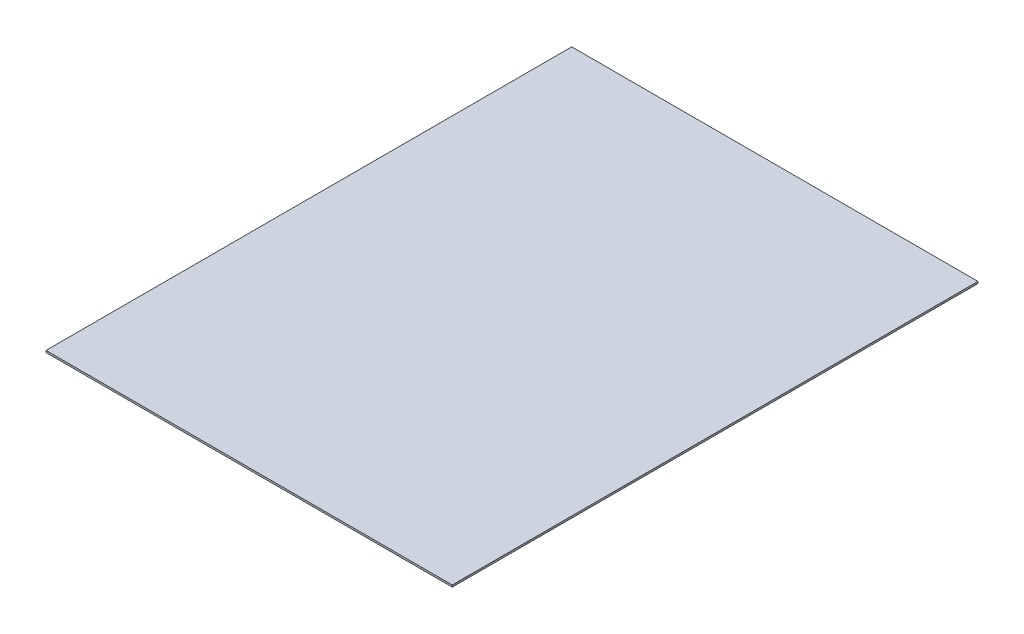
SolidWorks part; units mm, degrees
ref_plane "Front Plane" through (0, 0, 0) normal (0, 0, 1) x (1, 0, 0)
ref_plane "Top Plane" through (0, 0, 0) normal (0, 1, 0) x (1, 0, 0)
ref_plane "Right Plane" through (0, 0, 0) normal (1, 0, 0) x (0, 0, -1)
sketch "Sketch1" plane through (0, 0, 0) normal (0, 1, 0) x (1, 0, 0)
  line L1 (107.95, 139.7) -> (-107.95, 139.7)
  line L2 (107.95, 139.7) -> (107.95, -139.7)
  line L3 (107.95, -139.7) -> (-107.95, -139.7)
  line L4 (-107.95, 139.7) -> (-107.95, -139.7)
  line L5 (107.95, 139.7) -> (-107.95, -139.7) construction
  line L6 (107.95, -139.7) -> (-107.95, 139.7) construction
  point P0 (0, 0)
  dimension "D1" = 215.9
  dimension "D2" = 279.4
extrude "Boss-Extrude1" add sketch "Sketch1" along normal blind 1
